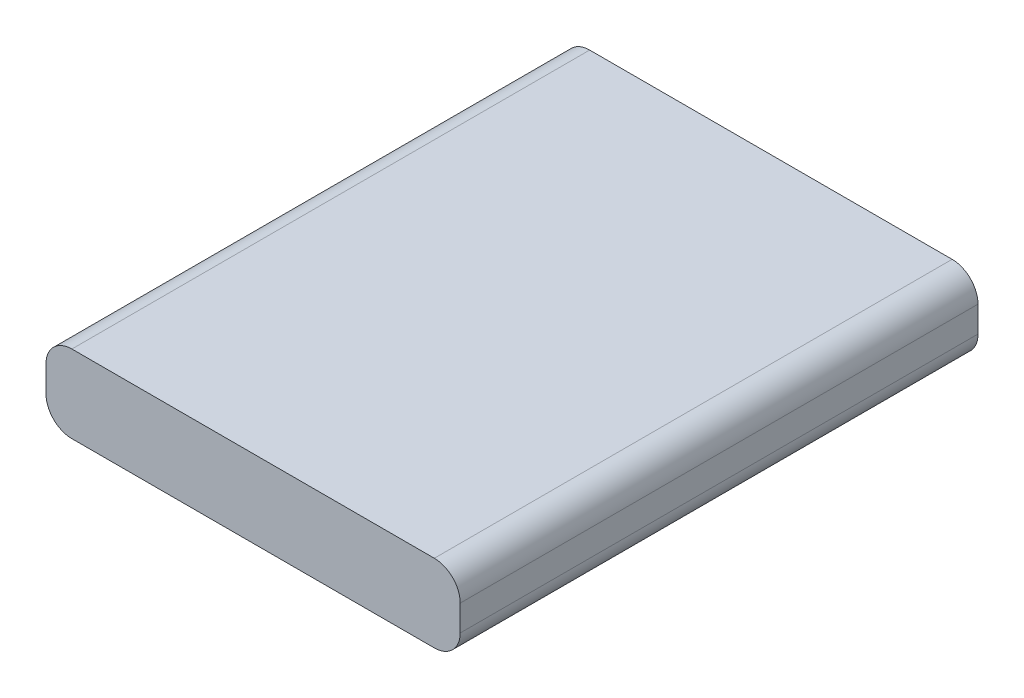
SolidWorks part; units mm, degrees
ref_plane "Front Plane" through (0, 0, 0) normal (0, 0, 1) x (1, 0, 0)
ref_plane "Top Plane" through (0, 0, 0) normal (0, 1, 0) x (1, 0, 0)
ref_plane "Right Plane" through (0, 0, 0) normal (1, 0, 0) x (0, 0, -1)
sketch "Sketch1" plane through (0, 0, 0) normal (0, 1, 0) x (1, 0, 0)
  line L1 (-24, -30) -> (24, -30)
  line L2 (-24, -30) -> (-24, 30)
  line L3 (-24, 30) -> (24, 30)
  line L4 (24, -30) -> (24, 30)
  line L5 (-24, -30) -> (24, 30) construction
  line L6 (-24, 30) -> (24, -30) construction
  point P0 (0, 0)
  dimension "D1" = 48
  dimension "D2" = 60
extrude "Boss-Extrude1" add sketch "Sketch1" along normal blind 9
fillet "Fillet1" radius 3 4 edges at (-24, 0, 0) (-24, 9, 0) (24, 0, 0) (24, 9, 0)
